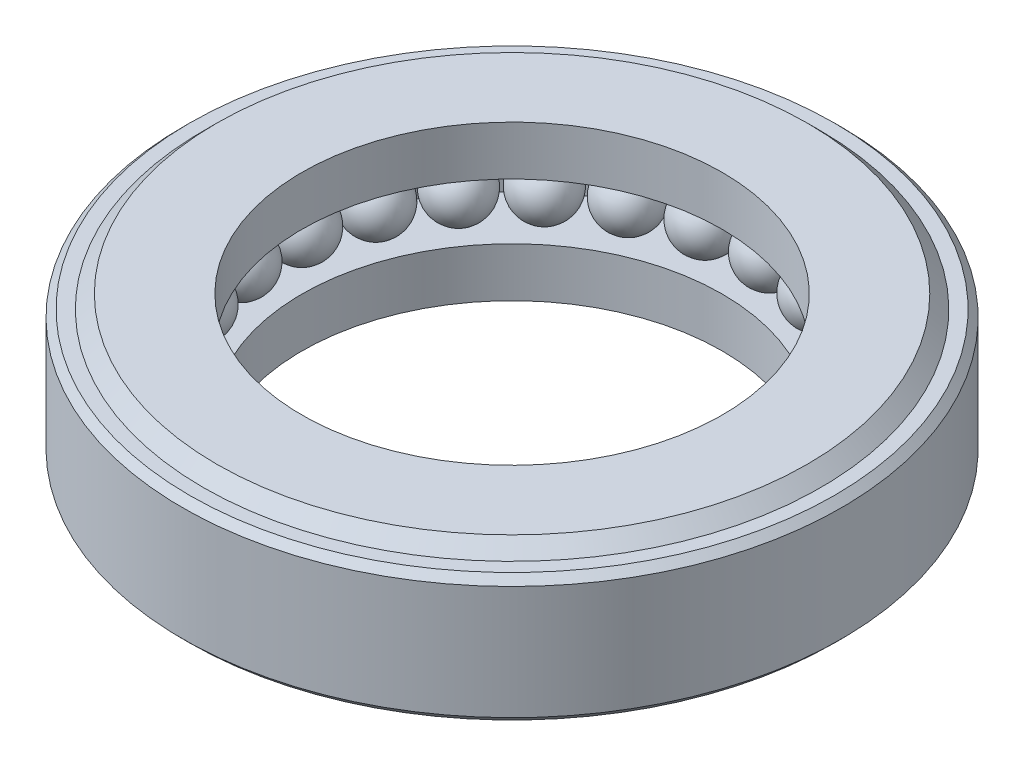
SolidWorks part; units mm, degrees
material "Plain Carbon Steel"
ref_plane "Front Plane" through (0, 0, 0) normal (0, 0, 1) x (1, 0, 0)
ref_plane "Top Plane" through (0, 0, 0) normal (0, 1, 0) x (1, 0, 0)
ref_plane "Right Plane" through (0, 0, 0) normal (1, 0, 0) x (0, 0, -1)
sketch "Sketch2" plane through (0, 0, 0) normal (0, 0, 1) x (1, 0, 0)
  line L0 (0, 0) -> (0, 0.9495) construction
  line L1 (0, 0) -> (3.3958, 0) construction
  line L2 (2.94, 0.5067) -> (2.94, -0.5067)
  line L3 (2.8767, -0.57) -> (2.755, -0.57)
  line L4 (2.755, -0.57) -> (2.635, -0.69)
  line L5 (2.635, -0.69) -> (1.875, -0.69)
  line L6 (2.8767, 0.57) -> (2.755, 0.57)
  line L7 (2.755, 0.57) -> (2.635, 0.69)
  line L8 (2.635, 0.69) -> (1.875, 0.69)
  line L9 (2.94, 0.5067) -> (2.8767, 0.57)
  line L10 (2.94, -0.5067) -> (2.8767, -0.57)
  line L11 (2.44, 0.25) -> (2.44, -0.25)
  line L12 (2.44, 0.25) -> (1.875, 0.25)
  line L13 (1.875, 0.25) -> (1.875, 0.69)
  line L14 (2.44, -0.25) -> (1.875, -0.25)
  line L15 (1.875, -0.25) -> (1.875, -0.69)
  point P5 (2.94, 0.57)
  point P6 (2.94, -0.57)
  dimension "D1" = 1.14
  dimension "D2" = 2.94
  dimension "D3" = 2.755
  dimension "D4" = 2.635
  dimension "D5" = 1.38
  dimension "D6" = 0.0633
  dimension "D7" = 45
  dimension "D8" = 0.0633
  dimension "D9" = 45
  dimension "D10" = 0.5
  dimension "D11" = 1.875
  dimension "D12" = 0.5
revolve "Revolve1" add sketch "Sketch2" angle 360 about L0
sketch "Sketch3" plane through (0, 0, 0) normal (0, 0, 1) x (1, 0, 0)
  line L0 (2.165, 0.26) -> (2.165, -0.26)
  line L1 (0, 0) -> (3.6519, 0) construction
  arc A0 (2.165, -0.26) -> (2.165, 0.26) centre (2.165, 0) ccw
  dimension "D3" = 0.52
  dimension "D2" = 2.165
revolve "Revolve2" add sketch "Sketch3" angle 360 about L0
pattern_circular "CirPattern1" count 25 over 360 about axis through (0, 0, 0) along (0, 1, 0) of "Revolve2"
